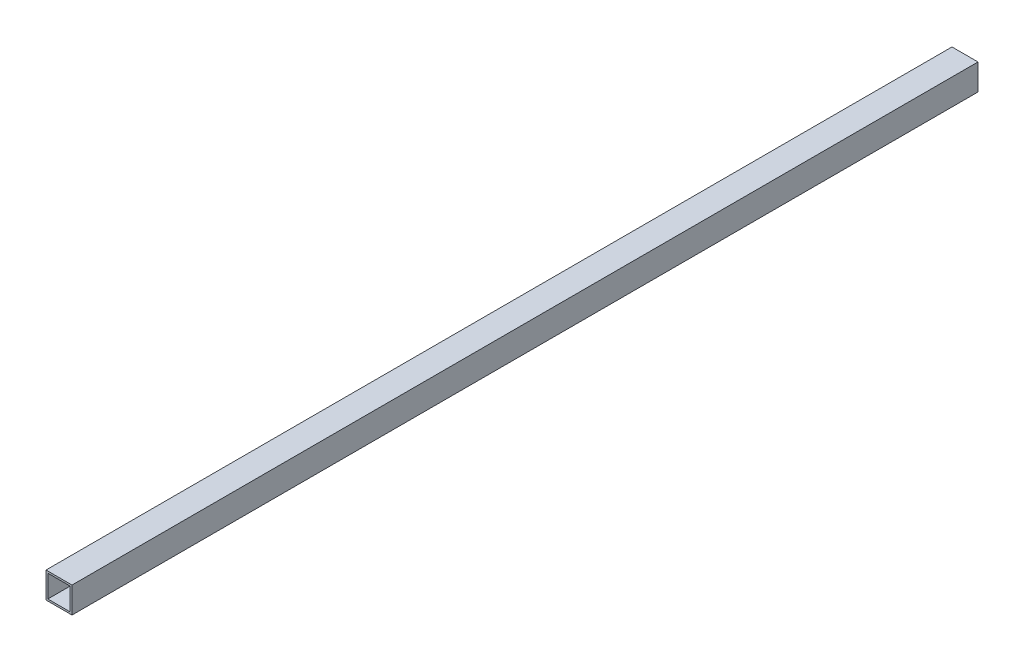
SolidWorks part; units mm, degrees
material "6061 Alloy"
ref_plane "Front Plane" through (0, 0, 0) normal (0, 0, 1) x (1, 0, 0)
ref_plane "Top Plane" through (0, 0, 0) normal (0, 1, 0) x (1, 0, 0)
ref_plane "Right Plane" through (0, 0, 0) normal (1, 0, 0) x (0, 0, -1)
sketch "Sketch1" plane through (0, 0, 0) normal (0, 0, 1) x (1, 0, 0)
  line L0 (-7.3, 7.3) -> (7.3, 7.3)
  line L1 (-8.5, -8.5) -> (8.5, -8.5)
  line L2 (-8.5, -8.5) -> (-8.5, 8.5)
  line L3 (-8.5, 8.5) -> (8.5, 8.5)
  line L4 (8.5, -8.5) -> (8.5, 8.5)
  line L5 (-8.5, -8.5) -> (8.5, 8.5) construction
  line L6 (-8.5, 8.5) -> (8.5, -8.5) construction
  line L7 (7.3, -7.3) -> (7.3, 7.3)
  line L8 (-7.3, -7.3) -> (7.3, -7.3)
  line L9 (-7.3, -7.3) -> (-7.3, 7.3)
  point P0 (0, 0)
  dimension "D1" = 17
  dimension "D2" = 17
  dimension "D3" = 1.2
extrude "Boss-Extrude1" add sketch "Sketch1" along normal blind 592
